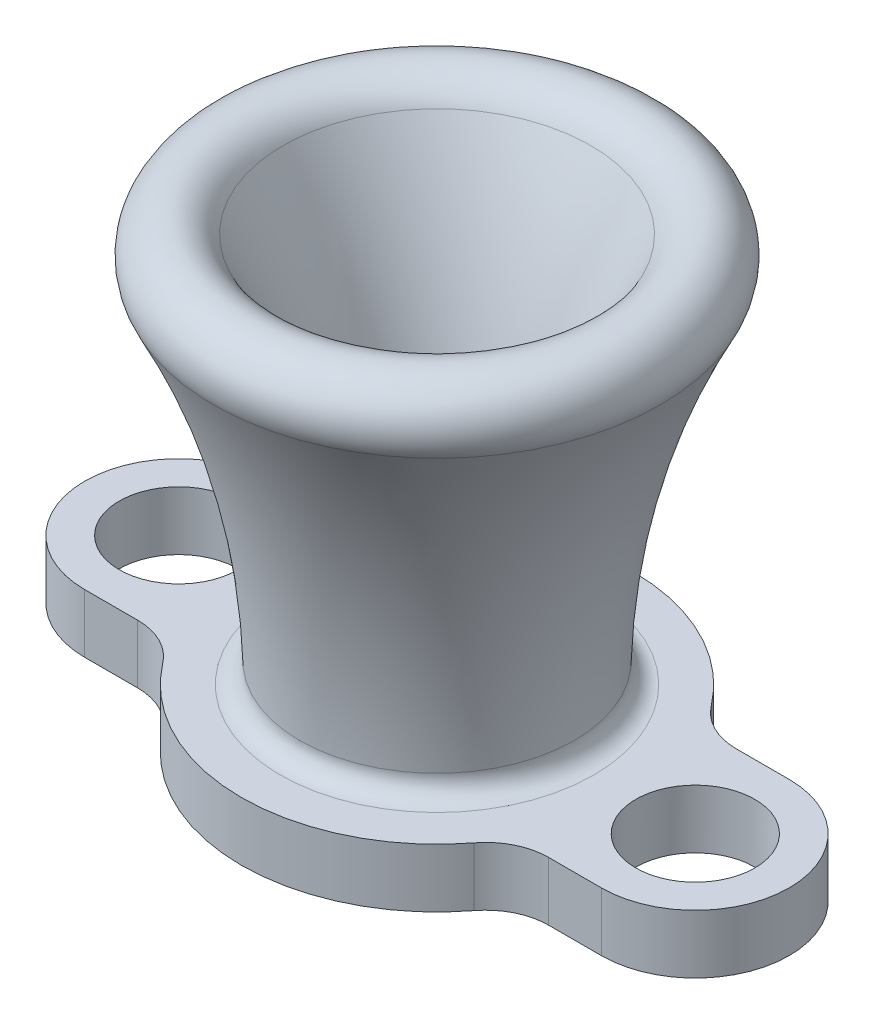
SolidWorks part; units mm, degrees
ref_plane "Front Plane" through (0, 0, 0) normal (0, 0, 1) x (1, 0, 0)
ref_plane "Top Plane" through (0, 0, 0) normal (0, 1, 0) x (1, 0, 0)
ref_plane "Right Plane" through (0, 0, 0) normal (1, 0, 0) x (0, 0, -1)
sketch "Sketch1" plane through (0, 0, 0) normal (0, 0, 1) x (1, 0, 0)
  line L0 (-36.7109, 0) -> (-6.2397, 15.8125) construction
  line L1 (-5.5563, 0) -> (-14.2875, 0)
  line L2 (-14.2875, 0) -> (-14.2875, -2.3812)
  line L3 (-14.2875, -2.3812) -> (-2.3813, -2.3812)
  line L4 (-2.3813, -2.3812) -> (-2.3813, 0)
  line L5 (-2.3813, -2.3812) -> (2.3813, -2.3812) construction
  line L6 (0, -2.3813) -> (0, 10.3187) construction
  line L7 (0, 10.3187) -> (-3.9688, 10.3187) construction
  line L8 (0, 10.3187) -> (3.9687, 10.3187) construction
  line L9 (-7.6488, 16.6687) -> (0, 16.6687) construction
  line L10 (0, 16.6687) -> (0, 10.3187) construction
  arc A0 (-5.5563, 0) -> (-9.0579, 14.35) centre (-36.7109, 0) ccw
  arc A1 (-2.3813, 0) -> (-6.2397, 15.8125) centre (-36.7109, 0) ccw
  arc A2 (-6.2397, 15.8125) -> (-9.0579, 14.35) centre (-7.6488, 15.0813) ccw
  dimension "D3" = 3.175
  dimension "D1" = 2.3813
  dimension "D2" = 4.7625
  dimension "D4" = 7.9375
  dimension "D5" = 12.7
  dimension "D6" = 28.575
  dimension "D7" = 19.05
revolve "Revolve1" add sketch "Sketch1" angle 360 about L6
sketch "Sketch2" plane through (0, -2.3812, 0) normal (0, -1, 0) x (1, 0, 0)
  line L0 (0, 7.9375) -> (0, 0) construction
  line L1 (14.2875, 0) -> (-14.2875, 0) construction
  line L2 (-10.4775, 3.81) -> (-6.9633, 3.81)
  line L3 (-10.4775, -3.81) -> (-6.9633, -3.81)
  line L4 (10.4775, -3.81) -> (6.9633, -3.81)
  line L5 (10.4775, 3.81) -> (6.9633, 3.81)
  arc A0 (-10.4775, 3.81) -> (-10.4775, -3.81) centre (-10.4775, 0) ccw
  circle A1 centre (0, 0) radius 14.2875 construction
  arc A2 (-6.9633, 3.81) -> (6.9633, 3.81) centre (0, 0) cw
  circle A3 centre (-10.4775, 0) radius 2.413
  arc A4 (-6.9633, -3.81) -> (6.9633, -3.81) centre (0, 0) ccw
  circle A5 centre (10.4775, 0) radius 2.413
  arc A6 (10.4775, 3.81) -> (10.4775, -3.81) centre (10.4775, 0) cw
  dimension "D2" = 4.826
  dimension "D3" = 7.9375
  dimension "D1" = 20.955
extrude "Cut-Extrude1" cut sketch "Sketch2" against normal up to surface (2.3812 mm away) flip side to cut up to face at (14.2875, 0, 0)
fillet "Fillet1" radius 2.54 4 edges at (-6.9633, -1.1906, 3.81) (6.9633, -1.1906, 3.81) (6.9633, -1.1906, -3.81) (-6.9633, -1.1906, -3.81)
fillet "Fillet2" radius 0.7937 1 edges at (5.5563, 0, 0)
